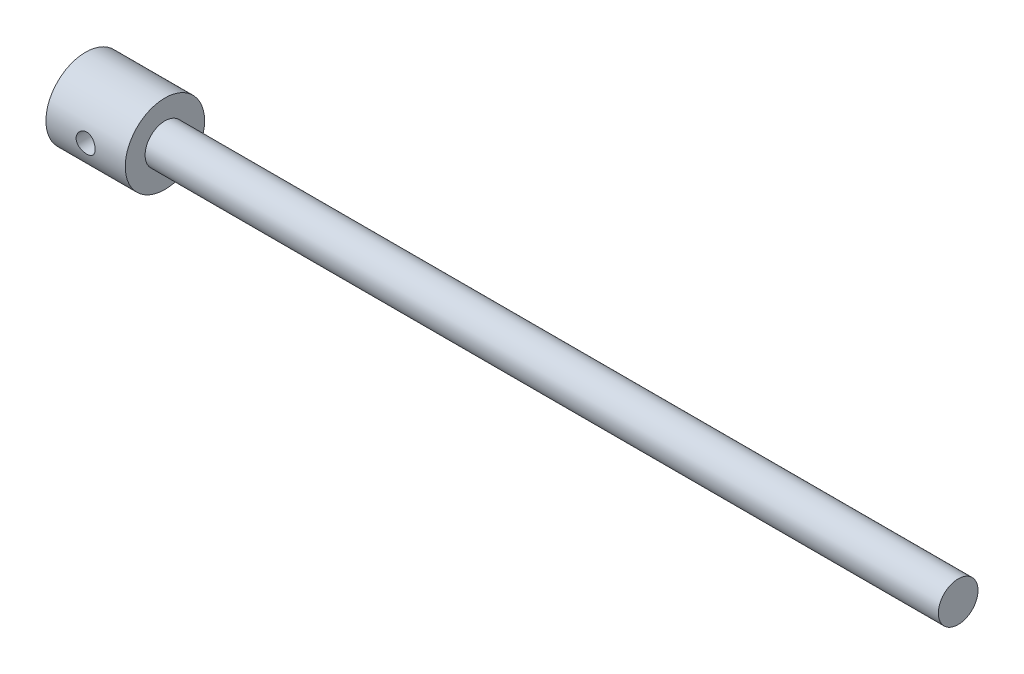
SolidWorks part; units mm, degrees
ref_plane "Front Plane" through (0, 0, 0) normal (0, 0, 1) x (1, 0, 0)
ref_plane "Top Plane" through (0, 0, 0) normal (0, 1, 0) x (1, 0, 0)
ref_plane "Right Plane" through (0, 0, 0) normal (1, 0, 0) x (0, 0, -1)
sketch "Sketch1" plane through (0, 0, 0) normal (1, 0, 0) x (0, 0, -1)
  circle A0 centre (0, 0) radius 25
  dimension "D1" = 50
extrude "Boss-Extrude1" add sketch "Sketch1" along normal blind 50 contours A0
sketch "Sketch2" plane through (0, 0, 0) normal (0, 0, 1) x (1, 0, 0)
  line L0 (0, 25) -> (0, -25) construction
  circle A0 centre (25, 0) radius 6
  dimension "D1" = 12
  dimension "D2" = 25
extrude "Cut-Extrude1" cut sketch "Sketch2" against normal blind 60 and the other way through all
sketch "Sketch3" plane through (50, 0, 0) normal (1, 0, 0) x (0, 0, -1)
  circle A0 centre (0, 0) radius 12.5
  circle A1 centre (0, 0) radius 25 construction
  dimension "D1" = 25
extrude "Boss-Extrude2" add sketch "Sketch3" along normal blind 500
cosmetic thread "Cosmetic Thread1" parameters "D1"=5, "D2"=21.797
cosmetic thread "Cosmetic Thread2" parameters "D1"=5, "D2"=21.797
